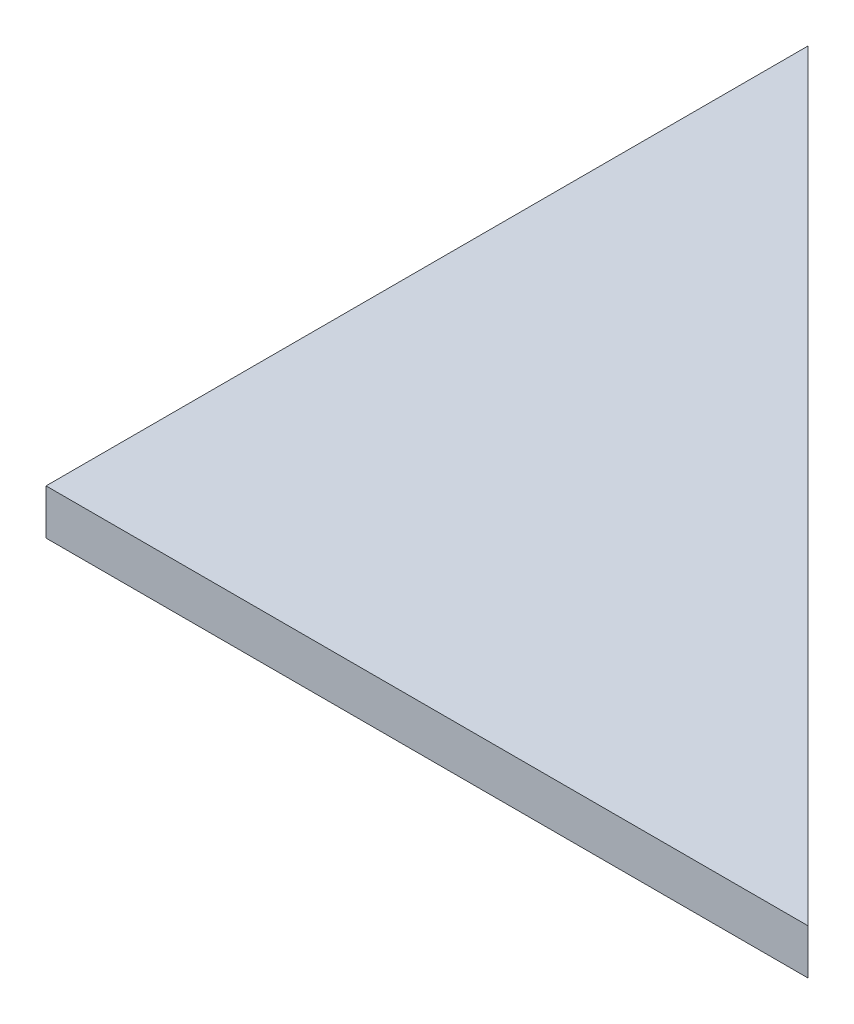
SolidWorks part; units mm, degrees
ref_plane "Front" through (0, 0, 0) normal (0, 0, 1) x (1, 0, 0)
ref_plane "Top" through (0, 0, 0) normal (0, 1, 0) x (1, 0, 0)
ref_plane "Right" through (0, 0, 0) normal (1, 0, 0) x (0, 0, -1)
sketch "Sketch1" plane through (0, 0, 0) normal (0, 1, 0) x (1, 0, 0)
  line L0 (0, 0) -> (50.5, 0)
  line L1 (50.5, 0) -> (0, 50.5)
  line L2 (0, 50.5) -> (0, 0)
  dimension "D1" = 50.5
extrude "Boss-Extrude1" add sketch "Sketch1" along normal blind 3
sketch "Sketch2" plane through (0, 0, 0) normal (0, 1, 0) x (1, 0, 0)
  line L0 (-4, -4) -> (60.1569, -4)
  line L1 (60.1569, -4) -> (-4, 60.1569)
  line L2 (-4, 60.1569) -> (-4, -4)
  line L5 (-4, -4) -> (0, 0) construction
  line L6 (50.5, 0) -> (0, 50.5) construction
  line L7 (50.5, -4) -> (50.5, 0) construction
  line L8 (50.5, 0) -> (53.3284, 2.8284) construction
  point P5 (60.0567, -4)
  dimension "D1" = 4
ref_plane "Plane1" through (0, 0, 0) normal (-0.7071, 0, -0.7071) x (-0.7071, 0, 0.7071)
